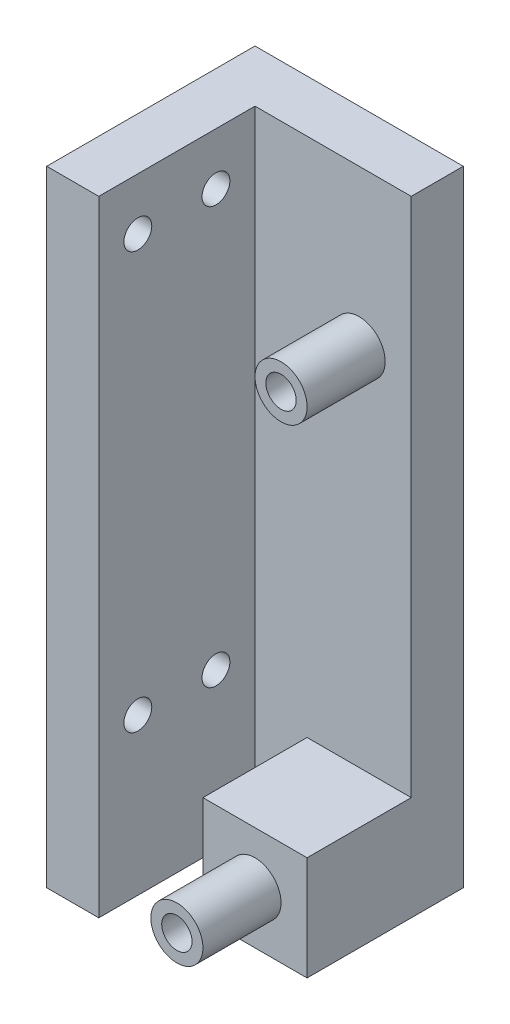
SolidWorks part; units mm, degrees
ref_plane "Front Plane" through (0, 0, 0) normal (0, 0, 1) x (1, 0, 0)
ref_plane "Top Plane" through (0, 0, 0) normal (0, 1, 0) x (1, 0, 0)
ref_plane "Right Plane" through (0, 0, 0) normal (1, 0, 0) x (0, 0, -1)
sketch "Sketch1" plane through (0, 0, 0) normal (0, 0, 1) x (1, 0, 0)
  line L1 (0, 0) -> (25.4, 0)
  line L2 (0, 0) -> (0, 76.2)
  line L3 (0, 76.2) -> (25.4, 76.2)
  line L4 (25.4, 0) -> (25.4, 76.2)
  dimension "D1" = 76.2
  dimension "D2" = 25.4
extrude "Boss-Extrude1" add sketch "Sketch1" against normal blind 25.4
sketch "Sketch10" plane through (25.4, 0, 0) normal (1, 0, 0) x (0, 0, -1)
  line L0 (25.4, 76.2) -> (0, 76.2) construction
  line L1 (19.05, 76.2) -> (0, 76.2)
  line L2 (19.05, 76.2) -> (19.05, 0)
  line L3 (19.05, 0) -> (0, 0)
  line L4 (0, 76.2) -> (0, 0)
  line L5 (25.4, 0) -> (0, 0) construction
  line L6 (25.4, 0) -> (25.4, 76.2) construction
  line L8 (0, 0) -> (0, 76.2) construction
  dimension "D1" = 6.35
extrude "Cut-Extrude5" cut sketch "Sketch10" against normal offset from surface (19.05 mm away) 6.35 up to face at (0, 38.1, -12.7)
sketch "Sketch12" plane through (0, 0, -25.4) normal (0, 0, -1) x (-1, 0, 0)
  line L0 (-25.4, 76.2) -> (0, 76.2) construction
  line L1 (-25.4, 0) -> (-25.4, 76.2) construction
  circle A1 centre (-19.05, 57.15) radius 3.175
  circle A2 centre (-19.05, 57.15) radius 1.85
  dimension "D2" = 6.35
  dimension "D4" = 3.7
  dimension "D1" = 19.05
  dimension "D3" = 6.35
extrude "Boss-Extrude2" add sketch "Sketch12" against normal blind 9.525 from surface at -6.35 starting at face at (15.875, 38.1, -19.05)
sketch "Sketch13" plane through (0, 0, -25.4) normal (0, 0, -1) x (-1, 0, 0)
  line L1 (-25.4, 0) -> (-12.7, 0)
  line L3 (-25.4, 12.7) -> (-12.7, 12.7)
  line L4 (-12.7, 0) -> (-12.7, 12.7)
  line L5 (-25.4, 12.7) -> (-25.4, 0)
  dimension "D2" = 12.7
  dimension "D3" = 12.7
extrude "Boss-Extrude3" add sketch "Sketch13" against normal blind 12.7 from surface at -6.35 starting at face at (19.05, 60.325, -19.05)
sketch "Sketch14" plane through (0, 0, -6.35) normal (0, 0, 1) x (1, 0, 0)
  line L1 (25.4, 0) -> (12.7, 0) construction
  line L2 (25.4, 12.7) -> (25.4, 76.2) construction
  circle A0 centre (19.05, 6.35) radius 1.85
  circle A1 centre (19.05, 6.35) radius 3.175
  circle A3 centre (19.05, 57.15) radius 1.85 construction
  circle A4 centre (19.05, 57.15) radius 3.175 construction
  dimension "D1" = 6.35
  dimension "D2" = 6.35
extrude "Boss-Extrude4" add sketch "Sketch14" along normal blind 9.525
sketch "Sketch15" plane through (6.35, 0, 0) normal (1, 0, 0) x (0, 0, -1)
  line L1 (19.05, 76.2) -> (0, 76.2) construction
  line L2 (0, 76.2) -> (0, 0) construction
  line L3 (19.05, 12.7) -> (19.05, 76.2) construction
  line L4 (0, 0) -> (19.05, 0) construction
  circle A0 centre (4.7625, 69.85) radius 1.7
  circle A1 centre (14.2875, 69.85) radius 1.7
  circle A2 centre (4.7625, 19.05) radius 1.7
  circle A3 centre (14.2875, 19.05) radius 1.7
  dimension "D2" = 6.35
  dimension "D1" = 3.4
  dimension "D3" = 4.7625
  dimension "D4" = 4.7625
  dimension "D5" = 19.05
extrude "Cut-Extrude6" cut sketch "Sketch15" against normal through all
equation "\"D4@Sketch12\"= 3.7mm"
equation "\"D1@Boss-Extrude1\"=(0.375+15.7mm)+0.25+0.25"
equation "\"tightTol\"= 0.005in"
equation "\"normTol\"= 0.01in"
equation "\"looseTol\"= 0.02in"
equation "\"D1@Sketch15\"=3.4mm"
